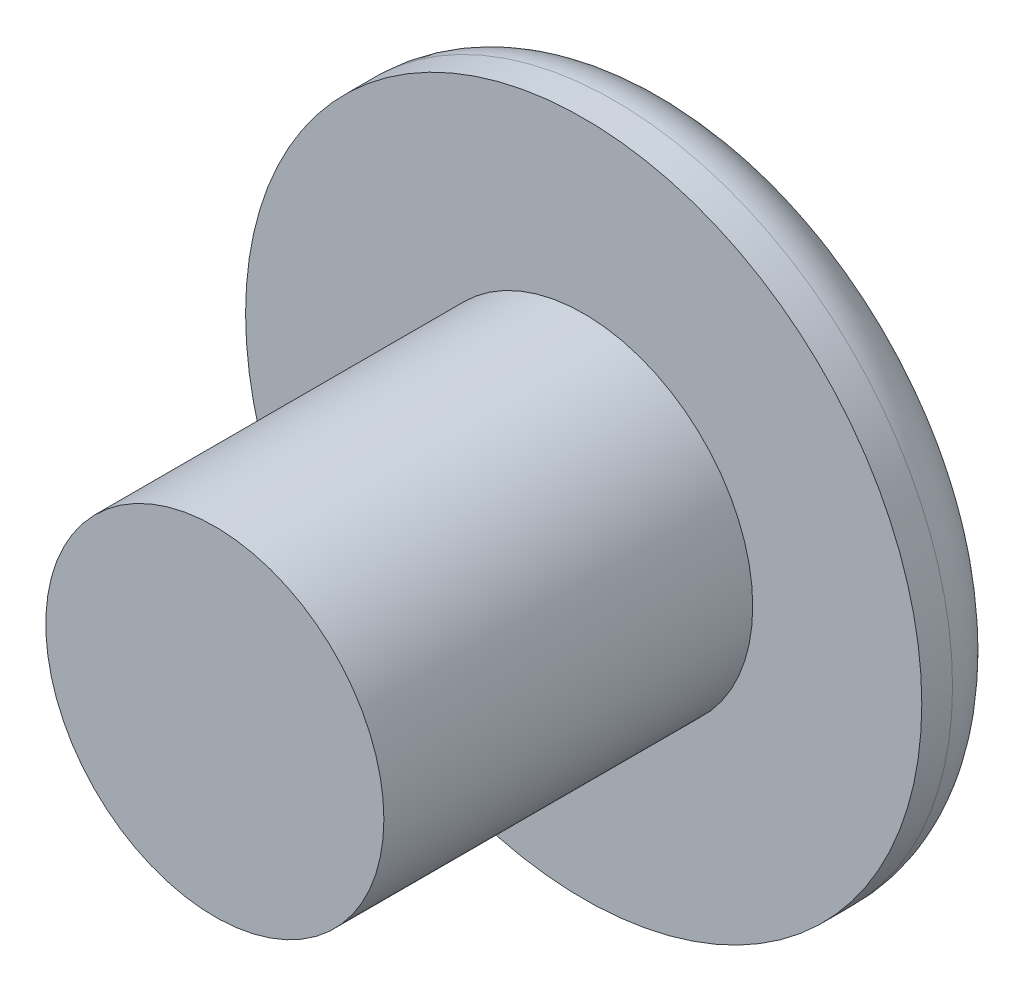
SolidWorks part; units mm, degrees
ref_plane "Front Plane" through (0, 0, 0) normal (0, 0, 1) x (1, 0, 0)
ref_plane "Top Plane" through (0, 0, 0) normal (0, 1, 0) x (1, 0, 0)
ref_plane "Right Plane" through (0, 0, 0) normal (1, 0, 0) x (0, 0, -1)
sketch "Sketch1" plane through (0, 0, 0) normal (0, 0, 1) x (1, 0, 0)
  circle A0 centre (0, 0) radius 11
  dimension "D1" = 22
extrude "Boss-Extrude1" add sketch "Sketch1" along normal blind 3
sketch "Sketch2" plane through (0, 0, 3) normal (0, 0, 1) x (1, 0, 0)
  circle A0 centre (0, 0) radius 5.5
  dimension "D1" = 11
extrude "Boss-Extrude2" add sketch "Sketch2" along normal blind 12
fillet "Fillet1" radius 2 1 edges at (11, 0, 0)
